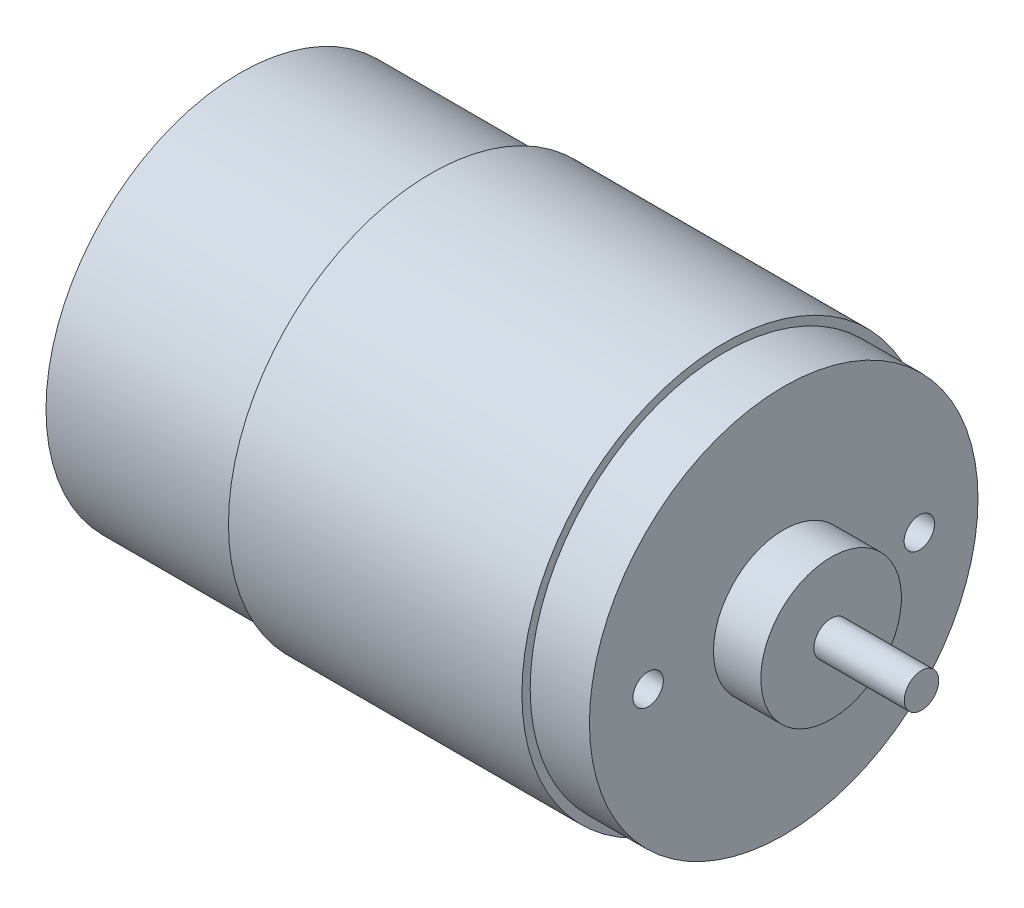
SolidWorks part; units mm, degrees
ref_plane "Front Plane" through (0, 0, 0) normal (0, 0, 1) x (1, 0, 0)
ref_plane "Top Plane" through (0, 0, 0) normal (0, 1, 0) x (1, 0, 0)
ref_plane "Right Plane" through (0, 0, 0) normal (1, 0, 0) x (0, 0, -1)
sketch "Sketch1" plane through (0, 0, 0) normal (0, 0, 1) x (1, 0, 0)
  line L0 (-37.6388, 0) -> (28.1887, 0) construction
  line L1 (-29.8041, 0) -> (-29.8041, 1.5346)
  line L2 (-29.8041, 1.5346) -> (-28.9156, 1.5346)
  line L3 (-28.9156, 1.5346) -> (-28.9156, 2.6654)
  line L4 (-28.9156, 2.6654) -> (-27.6233, 2.6654)
  line L5 (-27.6233, 2.6654) -> (-27.6233, 4.7654)
  line L6 (-27.6233, 4.7654) -> (-26.6944, 5.6943)
  line L7 (-26.6944, 5.6943) -> (-24.6479, 5.6943)
  line L8 (-24.6479, 5.6943) -> (-24.6479, 17.907)
  line L9 (-24.6479, 17.907) -> (-7.0711, 17.907)
  line L10 (-7.0711, 17.907) -> (-7.0711, 18.669)
  line L11 (-7.0711, 18.669) -> (19.9799, 18.669)
  line L12 (19.9799, 18.669) -> (19.9799, 17.907)
  line L13 (19.9799, 17.907) -> (25.4409, 17.907)
  line L14 (25.4409, 17.907) -> (25.4409, 6.477)
  line L15 (25.4409, 6.477) -> (29.8097, 6.477)
  line L16 (29.8097, 6.477) -> (29.8097, 1.5875)
  line L17 (29.8097, 1.5875) -> (38.1409, 1.5875)
  line L18 (38.1409, 1.5875) -> (38.1409, 0)
  line L19 (38.1409, 0) -> (-29.8041, 0)
  dimension "D1" = 37.338
  dimension "D2" = 35.814
  dimension "D3" = 35.814
  dimension "D4" = 12.954
  dimension "D5" = 3.175
  dimension "D6" = 67.945
  dimension "D7" = 8.3312
  dimension "D8" = 4.3688
  dimension "D9" = 5.461
  dimension "D10" = 27.051
  dimension "D11" = 50.0888
revolve "Revolve1" add sketch "Sketch1" angle 360 about L0
sketch "Sketch2" plane through (25.4409, 0, 0) normal (1, 0, 0) x (0, 0, -1)
  line L0 (0, 0) -> (-30.6002, 0) construction
  line L1 (0, 0) -> (0, 19.572) construction
  circle A0 centre (-12.4968, 0) radius 1.4
  circle A1 centre (12.4968, 0) radius 1.4
  dimension "D1" = 2.8
  dimension "D2" = 12.4968
extrude "Cut-Extrude1" cut sketch "Sketch2" against normal blind 6.35
